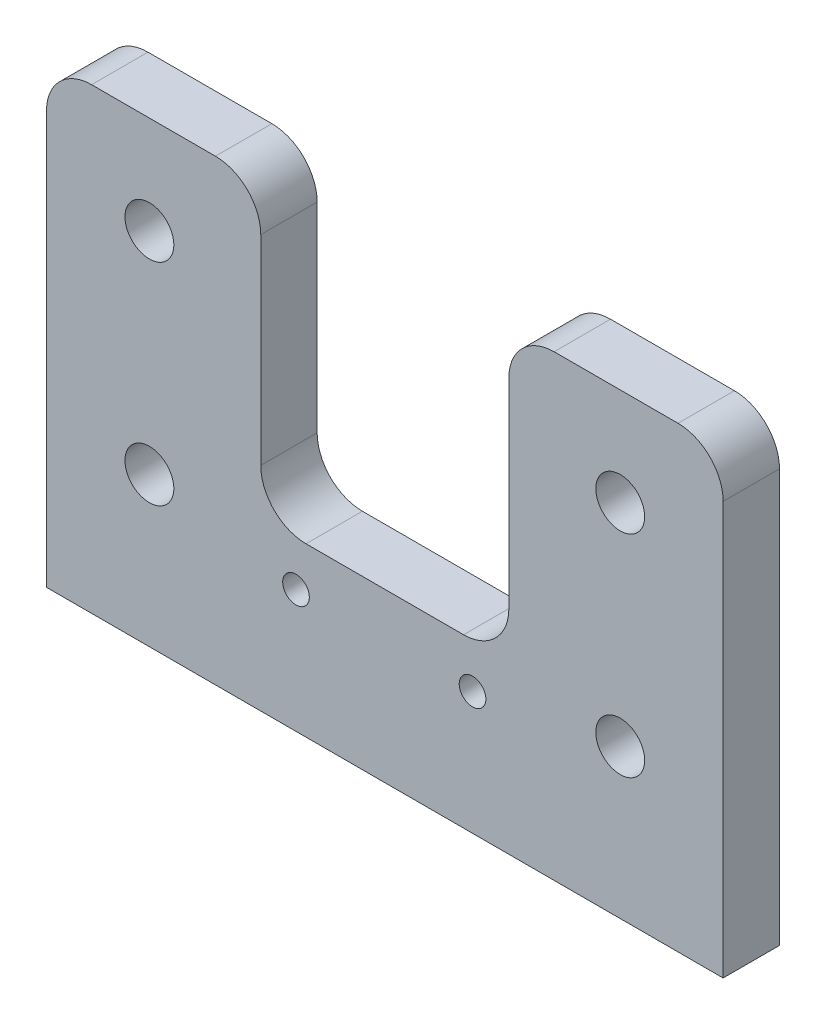
SolidWorks part; units mm, degrees
ref_plane "Front Plane" through (0, 0, 0) normal (0, 0, 1) x (1, 0, 0)
ref_plane "Top Plane" through (0, 0, 0) normal (0, 1, 0) x (1, 0, 0)
ref_plane "Right Plane" through (0, 0, 0) normal (1, 0, 0) x (0, 0, -1)
sketch "Sketch1" plane through (0, 0, 0) normal (0, 0, 1) x (1, 0, 0)
  line L1 (0, 0) -> (76.2, 0)
  line L2 (0, 0) -> (0, 51.562)
  line L3 (0, 51.562) -> (76.2, 51.562)
  line L4 (76.2, 0) -> (76.2, 51.562)
  dimension "D1" = 76.2
  dimension "D2" = 51.562
extrude "Boss-Extrude1" add sketch "Sketch1" along normal blind 6.35
sketch "Sketch2" plane through (0, 0, 6.35) normal (0, 0, 1) x (1, 0, 0)
  line L1 (0, 0) -> (76.2, 0) construction
  line L2 (52.07, 38.862) -> (24.13, 38.862)
  line L3 (38.1, 51.562) -> (38.1, 0) construction
  line L4 (76.2, 51.562) -> (0, 51.562) construction
  line L5 (0, 25.781) -> (76.2, 25.781) construction
  line L6 (0, 51.562) -> (0, 0) construction
  line L7 (76.2, 0) -> (76.2, 51.562) construction
  line L8 (0, 45.212) -> (76.2, 45.212) construction
  line L9 (52.07, 38.862) -> (52.07, 51.562)
  line L10 (52.07, 51.562) -> (24.13, 51.562)
  line L11 (24.13, 38.862) -> (24.13, 51.562)
  line L12 (52.07, 38.862) -> (24.13, 51.562) construction
  line L13 (52.07, 51.562) -> (24.13, 38.862) construction
  point P0 (38.1, 45.212)
  dimension "D1" = 12.7
  dimension "D2" = 27.94
extrude "Cut-Extrude1" cut sketch "Sketch2" against normal blind 9.906 contours L2 L11 L10 L9
fillet "Fillet1" radius 5.08 2 edges at (76.2, 51.562, 3.175) (0, 51.562, 3.175)
sketch "Sketch7" plane through (0, 0, 0) normal (0, 0, -1) x (-1, 0, 0)
  circle A0 centre (-11.588, 16.8) radius 2.75
  circle A1 centre (-64.612, 16.8) radius 2.75
extrude "Cut-Extrude2" cut sketch "Sketch7" against normal blind 127 contours A0 | A1
sketch "Sketch8" plane through (0, 0, 6.35) normal (0, 0, 1) x (1, 0, 0)
  line L0 (64.612, 16.8) -> (64.612, 51.562)
  line L1 (71.12, 51.562) -> (52.07, 51.562) construction
  line L2 (64.612, 51.562) -> (64.612, 40.562)
  circle A0 centre (64.612, 40.562) radius 2.75
extrude "Cut-Extrude4" cut sketch "Sketch8" against normal blind 32.416 contours L0 A0 | L0 A0
ref_plane "Plane2" through (38.1, 0, 0) normal (-1, 0, 0) x (0, 0, 1)
mirror "Mirror2" about plane through (38.1, 0, 0) normal (-1, 0, 0) of "Cut-Extrude4"
sketch "Sketch9" plane through (0, 0, 6.35) normal (0, 0, 1) x (1, 0, 0)
  line L1 (52.07, 38.862) -> (24.13, 38.862)
  line L2 (52.07, 38.862) -> (52.07, 18.862)
  line L3 (52.07, 18.862) -> (24.13, 18.862)
  line L4 (24.13, 38.862) -> (24.13, 18.862)
extrude "Cut-Extrude5" cut sketch "Sketch9" against normal blind 18.7
fillet "Fillet2" radius 5.1 4 edges at (24.13, 51.562, 3.175) (24.13, 18.862, 3.175) (52.07, 51.562, 3.175) (52.07, 18.862, 3.175)
sketch "Sketch10" plane through (0, 0, 6.35) normal (0, 0, 1) x (1, 0, 0)
  line L0 (76.2, 0) -> (47.98, 0) construction
  line L1 (0, 0) -> (76.2, 0) construction
  line L2 (47.98, 0) -> (47.98, 13.83) construction
  line L4 (0, 0) -> (28.1, 0) construction
  line L5 (28.1, 0) -> (28.1, 13.83) construction
  line L6 (0, 46.482) -> (0, 0) construction
  line L7 (76.2, 0) -> (76.2, 46.482) construction
  circle A4 centre (47.98, 13.83) radius 1.5
  circle A5 centre (28.1, 13.83) radius 1.5
  dimension "D1" = 3
  dimension "D2" = 3
  dimension "D4" = 13.83
  dimension "D5" = 28.1
  dimension "D6" = 28.22
  dimension "D3" = 13.83
extrude "Cut-Extrude6" cut sketch "Sketch10" against normal blind 10
